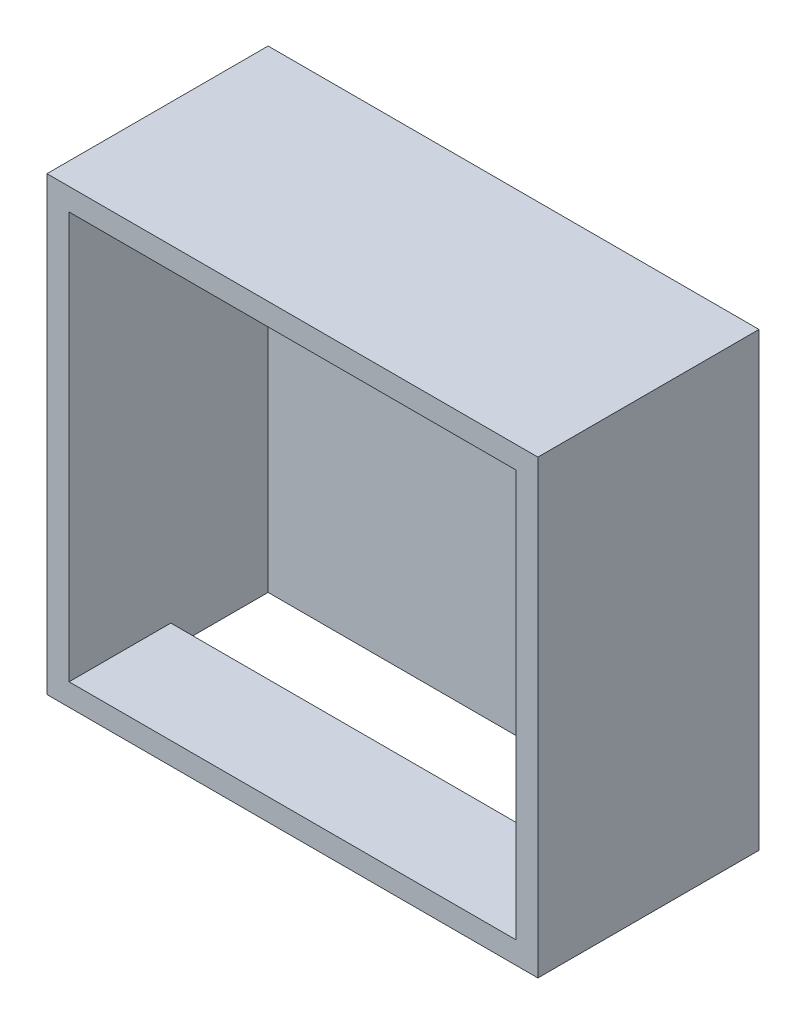
SolidWorks part; units mm, degrees
ref_plane "前基準面" through (0, 0, 0) normal (0, 0, 1) x (1, 0, 0)
ref_plane "上基準面" through (0, 0, 0) normal (0, 1, 0) x (1, 0, 0)
ref_plane "右基準面" through (0, 0, 0) normal (1, 0, 0) x (0, 0, -1)
sketch "草圖1" plane through (0, 0, 0) normal (0, 0, 1) x (1, 0, 0)
  line L1 (-77.5811, 47.4279) -> (23.4189, 47.4279)
  line L2 (-77.5811, 47.4279) -> (-77.5811, -44.5721)
  line L3 (-77.5811, -44.5721) -> (23.4189, -44.5721)
  line L4 (23.4189, 47.4279) -> (23.4189, -44.5721)
  line L5 (-82.5811, 52.4279) -> (28.4189, 52.4279)
  line L6 (-82.5811, 52.4279) -> (-82.5811, -49.5721)
  line L7 (-82.5811, -49.5721) -> (28.4189, -49.5721)
  line L8 (28.4189, 52.4279) -> (28.4189, -49.5721)
  dimension "D1" = 92
  dimension "D2" = 101
  dimension "D3" = 5
  dimension "D4" = 5
  dimension "D5" = 5
  dimension "D6" = 5
extrude "填料-伸長1" add sketch "草圖1" along normal blind 45
sketch "草圖2" plane through (0, 0, 0) normal (0, 0, -1) x (-1, 0, 0)
  line L1 (-28.4189, 52.4279) -> (82.5811, 52.4279)
  line L2 (-28.4189, 52.4279) -> (-28.4189, -49.5721)
  line L3 (-28.4189, -49.5721) -> (82.5811, -49.5721)
  line L4 (82.5811, 52.4279) -> (82.5811, -49.5721)
extrude "填料-伸長2" add sketch "草圖2" along normal blind 5
sketch "草圖3" plane through (0, -49.5721, 0) normal (0, -1, 0) x (1, 0, 0)
  line L1 (23.4189, 0) -> (-77.5811, 0)
  line L2 (23.4189, 0) -> (23.4189, 22)
  line L3 (23.4189, 22) -> (-77.5811, 22)
  line L4 (-77.5811, 0) -> (-77.5811, 22)
  line L6 (28.4189, -5) -> (-82.5811, -5) construction
  line L7 (-82.5811, 45) -> (-82.5811, -5) construction
  line L8 (28.4189, 45) -> (28.4189, -5) construction
  dimension "D1" = 5
  dimension "D2" = 22
  dimension "D3" = 5
  dimension "D4" = 5
extrude "除料-伸長4" cut sketch "草圖3" against normal blind 5
sketch "草圖4" plane through (0, 0, 0) normal (0, 0, 1) x (1, 0, 0)
  line L0 (-77.5811, 47.4279) -> (-77.5811, -49.5721) construction
  line L1 (23.4189, 47.4279) -> (-77.5811, 47.4279)
  line L2 (23.4189, 47.4279) -> (23.4189, 38.4279)
  line L3 (23.4189, 38.4279) -> (-77.5811, 38.4279)
  line L4 (-77.5811, 47.4279) -> (-77.5811, 38.4279)
  dimension "D1" = 9
extrude "填料-伸長3" add sketch "草圖4" along normal blind 8
